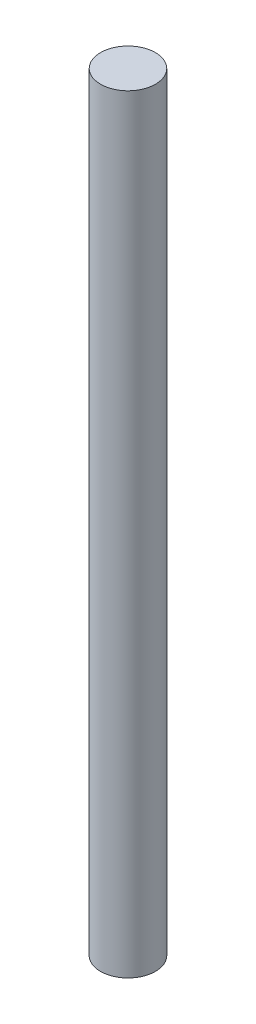
SolidWorks part; units mm, degrees
ref_plane "Plan de face" through (0, 0, 0) normal (0, 0, 1) x (1, 0, 0)
ref_plane "Plan de dessus" through (0, 0, 0) normal (0, 1, 0) x (1, 0, 0)
ref_plane "Plan de droite" through (0, 0, 0) normal (1, 0, 0) x (0, 0, -1)
sketch "Esquisse1" plane through (0, 0, 0) normal (0, 1, 0) x (1, 0, 0)
  circle A0 centre (0, 0) radius 5
  dimension "D1" = 10
extrude "Boss.-Extru.1" add sketch "Esquisse1" along normal blind 140
